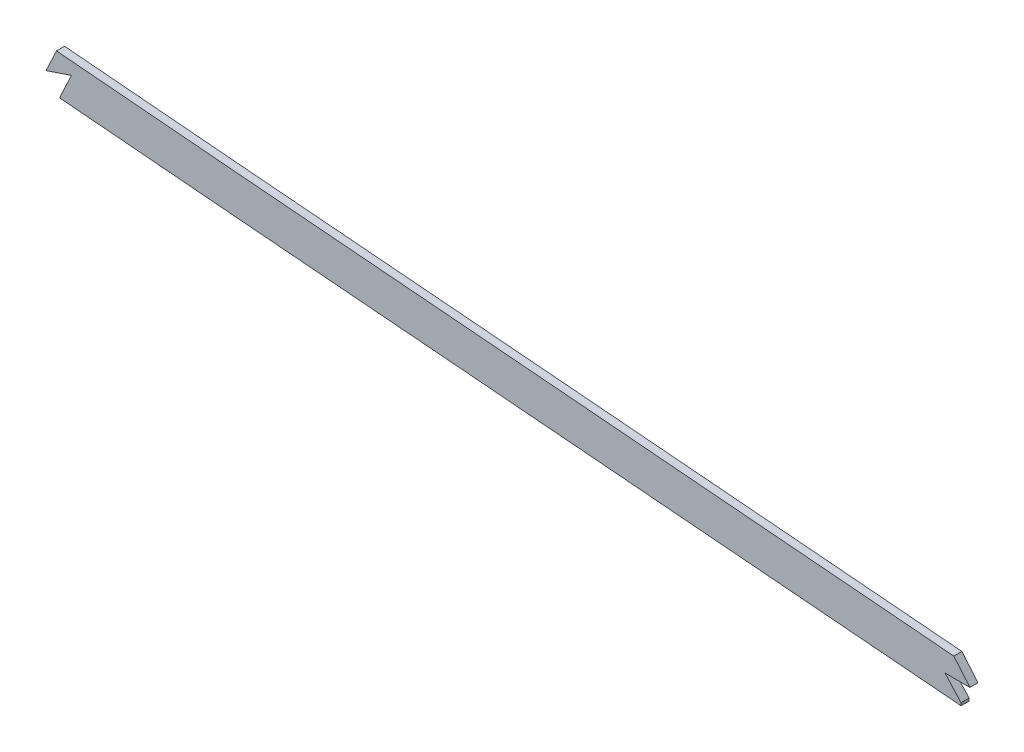
SolidWorks part; units mm, degrees
ref_plane "Front Plane" through (0, 0, 0) normal (0, 0, 1) x (1, 0, 0)
ref_plane "Top Plane" through (0, 0, 0) normal (0, 1, 0) x (1, 0, 0)
ref_plane "Right Plane" through (0, 0, 0) normal (1, 0, 0) x (0, 0, -1)
sketch "Sketch2" plane through (0, 0, 0) normal (0, 0, 1) x (1, 0, 0)
  line L0 (0, 0) -> (266.9553, 0) construction
  line L1 (825.5, 263.7287) -> (825.5, 174.6622)
  line L2 (2491.74, 117.5472) -> (2491.74, 52.664)
  spline S0 degree 5 poles (818.067, 264.7065) (827.0431, 263.4992) (836.0291, 262.3734) (845.0868, 261.3058) (891.3865, 256.087) (937.6862, 251.7792) (973.4521, 248.2277) (1071.9467, 239.0511) (1170.4413, 229.7315) (1231.7919, 224.5039) (1324.8993, 216.7906) (1418.0067, 209.0401) (1449.7429, 206.3618) (1636.9286, 190.5211) (1824.1143, 175.4092) (1979.9669, 164.2997) (2156.2686, 150.4144) (2332.5703, 133.8572) (2354.213, 131.7851) (2436.3555, 123.724) (2518.4981, 114.8591) (2579.4813, 107.7425) (2639.6368, 100.3834) (2699.7923, 92.6045) knots 77.930822 77.930822 77.930822 77.930822 77.930822 77.930822 82.465793 82.465793 82.465793 100.79329 100.79329 100.79329 131.098954 131.098954 131.098954 146.769198 146.769198 146.769198 223.533959 223.533959 223.533959 233.943117 233.943117 233.943117 264.216209 264.216209 264.216209 264.216209 264.216209 264.216209 weights 1 1 1 1 1 1 1 1 1 1 1 1 1 1 1 1 1 1 1 1 1 1 1 1
  spline S1 degree 1 poles (816.0355, 249.6025) (2697.8379, 77.4903) knots 0 0 1 1 construction
  spline S2 degree 3 poles (816.0355, 249.6025) (820.896, 248.9488) (830.6112, 247.6997) (845.2811, 245.9534) (860.0865, 244.2956) (879.8307, 242.1866) (904.37, 239.6983) (933.571, 236.8322) (962.6427, 234.0237) (991.7626, 231.242) (1021.072, 228.4759) (1060.3764, 224.797) (1109.513, 220.1844) (1168.5112, 214.8171) (1227.5001, 209.6621) (1306.1332, 203.0212) (1404.3615, 194.9207) (1522.2399, 184.9181) (1640.1829, 175.167) (1758.1654, 165.7576) (1876.1554, 156.5909) (1994.0875, 147.4533) (2092.2687, 139.6242) (2170.748, 133.0797) (2219.7717, 128.8422) (2258.984, 125.3472) (2288.3795, 122.6709) (2317.8122, 119.9317) (2347.5515, 117.1004) (2377.1599, 114.2101) (2406.4697, 111.269) (2435.8183, 108.2401) (2474.9139, 104.0902) (2523.7162, 98.6933) (2582.0419, 91.9123) (2640.0752, 84.8576) (2678.5742, 79.9814) (2697.8379, 77.4903) knots 77.930822 77.930822 77.930822 77.930822 79.386176 80.841531 82.296885 83.75224 86.662949 89.573658 92.484367 95.395077 98.305786 101.216495 107.037913 112.859332 118.68075 124.502168 136.145005 147.787842 159.430678 171.073515 182.716352 194.359189 206.002025 211.823444 217.644862 220.555571 223.46628 226.37699 229.287699 232.198408 235.109117 238.019826 240.930535 246.751954 252.573372 258.39479 264.216209 264.216209 264.216209 264.216209
  spline S3 degree 5 poles (818.067, -264.7065) (827.0431, -263.4992) (836.0291, -262.3734) (845.0868, -261.3058) (891.3865, -256.087) (937.6862, -251.7792) (973.4521, -248.2277) (1071.9467, -239.0511) (1170.4413, -229.7315) (1231.7919, -224.5039) (1324.8993, -216.7906) (1418.0067, -209.0401) (1449.7429, -206.3618) (1636.9286, -190.5211) (1824.1143, -175.4092) (1979.9669, -164.2997) (2156.2686, -150.4144) (2332.5703, -133.8572) (2354.213, -131.7851) (2436.3555, -123.724) (2518.4981, -114.8591) (2579.4813, -107.7425) (2639.6368, -100.3834) (2699.7923, -92.6045) knots 77.930822 77.930822 77.930822 77.930822 77.930822 77.930822 82.465793 82.465793 82.465793 100.79329 100.79329 100.79329 131.098954 131.098954 131.098954 146.769198 146.769198 146.769198 223.533959 223.533959 223.533959 233.943117 233.943117 233.943117 264.216209 264.216209 264.216209 264.216209 264.216209 264.216209 weights 1 1 1 1 1 1 1 1 1 1 1 1 1 1 1 1 1 1 1 1 1 1 1 1
  point P2 (0, 0)
  dimension "D1" = 818.067
  dimension "D2" = 825.5
  dimension "D3" = 2491.74
  dimension "D4" = 15.24
extrude "Boss-Extrude1" add sketch "Sketch2" along normal mid plane 3.175 contours L1 S2 L2 S0
fillet "Fillet1" radius 2.54 4 edges at (2491.74, 102.2148, 0) (825.5, 248.3644, 0)
sketch "Sketch3" plane through (0, 0, 1.5875) normal (0, 0, 1) x (1, 0, 0)
  line L0 (1201.6419, 227.2278) -> (1201.6419, 234.5422)
  line L1 (1201.6419, 227.2278) -> (1197.5086, 218.4497)
  line L2 (1197.5086, 218.4497) -> (1207.4958, 221.815)
  line L3 (1207.4958, 221.815) -> (1203.045, 212.262)
  line L4 (1554.7817, 197.537) -> (1561.1242, 190.0292)
  line L5 (1561.1242, 190.0292) -> (1551.3118, 190.0292)
  line L6 (1551.3118, 190.0292) -> (1557.6111, 183.0636)
  line L10 (1201.6419, 234.5422) -> (821.2181, 281.9295)
  line L11 (821.2181, 281.9295) -> (821.2181, 218.4497)
  line L12 (821.2181, 218.4497) -> (1203.045, 207.573)
  line L13 (1203.045, 207.573) -> (1203.045, 212.262)
  line L14 (1554.7817, 197.537) -> (1554.7817, 201.4162)
  line L15 (1554.7817, 201.4162) -> (2509.6886, 142.6714)
  line L16 (2509.6886, 142.6714) -> (2509.6886, 67.6076)
  line L17 (2509.6886, 67.6076) -> (1557.6111, 178.0642)
  line L18 (1557.6111, 178.0642) -> (1557.6111, 183.0636)
  spline S0 degree 5 poles (828.3591, 263.3639) (835.3006, 262.485) (842.2713, 261.6451) (849.2939, 260.8336) (893.49, 255.8914) (937.6862, 251.7793) (973.4521, 248.2278) (1071.9467, 239.0512) (1170.4413, 229.7316) (1231.792, 224.504) (1324.8993, 216.7907) (1418.0067, 209.0402) (1449.7429, 206.3619) (1636.9286, 190.5212) (1824.1143, 175.4092) (1979.967, 164.2997) (2156.2686, 150.4145) (2332.5703, 133.8572) (2354.213, 131.7851) (2393.888, 127.8915) (2433.5631, 123.8105) (2452.2167, 121.8477) (2470.8575, 119.8423) (2489.4775, 117.7961) knots 78.969534 78.969534 78.969534 78.969534 78.969534 78.969534 82.465793 82.465793 82.465793 100.79329 100.79329 100.79329 131.098954 131.098954 131.098954 146.769198 146.769198 146.769198 223.533959 223.533959 223.533959 233.943117 233.943117 233.943117 243.183575 243.183575 243.183575 243.183575 243.183575 243.183575 weights 1 1 1 1 1 1 1 1 1 1 1 1 1 1 1 1 1 1 1 1 1 1 1 1 construction
  point P0 (2509.6886, 142.6714)
extrude "Cut-Extrude1" cut sketch "Sketch3" against normal blind 7.62 contours L12 L13 L3 L2 L1 L0 L10 L11 | L15 L16 L17 L18 L6 L5 L4 L14
